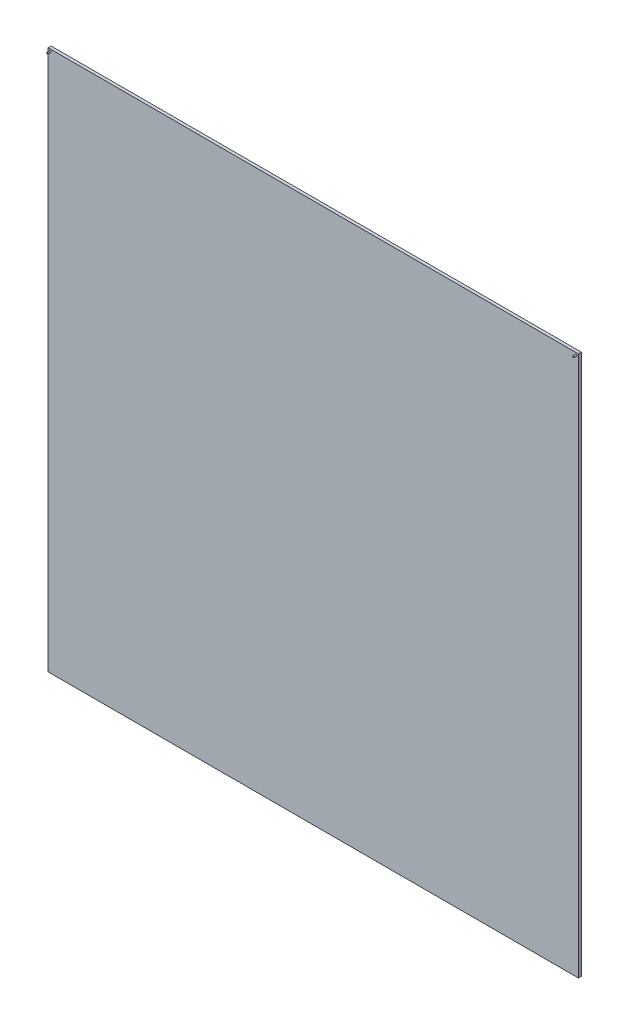
SolidWorks part; units mm, degrees
ref_plane "Front Plane" through (0, 0, 0) normal (0, 0, 1) x (1, 0, 0)
ref_plane "Top Plane" through (0, 0, 0) normal (0, 1, 0) x (1, 0, 0)
ref_plane "Right Plane" through (0, 0, 0) normal (1, 0, 0) x (0, 0, -1)
sketch "Sketch1" plane through (0, 0, 0) normal (0, 0, 1) x (1, 0, 0)
  line L0 (0, 1767.767) -> (1767.767, 0) construction
  line L1 (0, 0) -> (1767.767, 0) construction
  line L2 (0, 0) -> (0, 1767.767) construction
  line L3 (0, 1767.767) -> (1767.767, 1767.767) construction
  line L4 (1767.767, 0) -> (1767.767, 1767.767) construction
  line L5 (1767.767, 1767.767) -> (0, 0) construction
  line L7 (-15, 1782.767) -> (1782.767, 1782.767)
  line L8 (-15, 1782.767) -> (-15, -50)
  line L9 (-15, -50) -> (1782.767, -50)
  line L10 (1782.767, 1782.767) -> (1782.767, -50)
  dimension "D1" = 1767.767
  dimension "D2" = 1767.767
  dimension "D3" = 15
  dimension "D4" = 15
  dimension "D5" = 15
  dimension "D6" = 50
extrude "Boss-Extrude1" add sketch "Sketch1" along normal blind 10
sketch "Sketch2" plane through (0, 0, 10) normal (0, 0, 1) x (1, 0, 0)
  line L0 (0, 1767.767) -> (-15, 1782.767) construction
  line L1 (883.8835, 1782.767) -> (883.8835, -50) construction
  line L2 (-15, 1782.767) -> (1782.767, 1782.767) construction
  line L3 (-15, -50) -> (1782.767, -50) construction
  line L4 (1767.767, 1767.767) -> (1782.767, 1782.767) construction
  circle A0 centre (-7.5, 1775.267) radius 2.5
  circle A1 centre (1775.267, 1775.267) radius 2.5
  dimension "D1" = 5
extrude "Boss-Extrude2" add sketch "Sketch2" along normal blind 10
sketch "Sketch3" plane through (0, 0, 10) normal (0, 0, 1) x (1, 0, 0)
  line L1 (0, 1767.767) -> (1767.767, 1767.767) construction
  line L2 (0, 1767.767) -> (0, 0) construction
  line L3 (0, 0) -> (1767.767, 0) construction
  line L4 (1767.767, 1767.767) -> (1767.767, 0) construction
